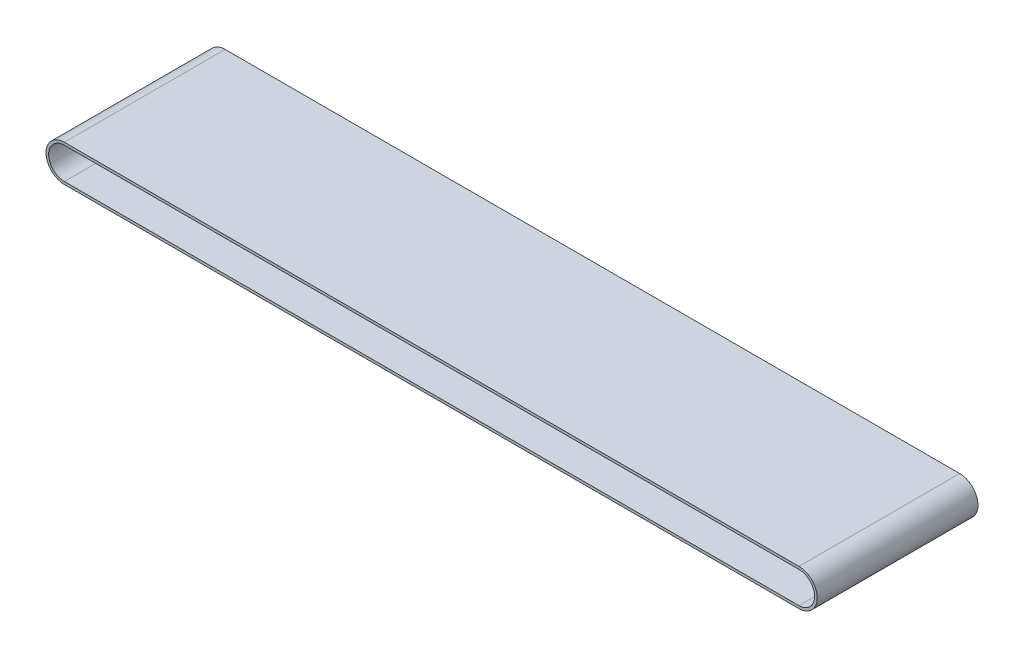
SolidWorks part; units mm, degrees
ref_plane "Front Plane" through (0, 0, 0) normal (0, 0, 1) x (1, 0, 0)
ref_plane "Top Plane" through (0, 0, 0) normal (0, 1, 0) x (1, 0, 0)
ref_plane "Right Plane" through (0, 0, 0) normal (1, 0, 0) x (0, 0, -1)
sketch "Sketch1" plane through (0, 0, 0) normal (0, 0, 1) x (1, 0, 0)
  line L202 (0, 61.4422) -> (0, -79.0701) construction
  line L203 (-281, 0) -> (281, 0) construction
  line L204 (-281, 12) -> (281, 12)
  line L205 (-281, -12) -> (281, -12)
  line L206 (-281, 0) -> (281, 0) construction
  line L207 (-281, 14) -> (281, 14)
  line L208 (-281, -14) -> (281, -14)
  arc A0 (-281, 12) -> (-281, -12) centre (-281, 0) ccw
  arc A1 (281, -12) -> (281, 12) centre (281, 0) ccw
  arc A2 (-281, 14) -> (-281, -14) centre (-281, 0) ccw
  arc A3 (281, -14) -> (281, 14) centre (281, 0) ccw
  point P4 (0, 0)
  point P11 (0, 0)
  point P16 (-295, 0)
  point P17 (295, 0)
  point P18 (-293, 0)
  dimension "D2" = 2
  dimension "D1" = 590
  dimension "D3" = 12
  dimension "D4" = 2
extrude "Boss-Extrude1" add sketch "Sketch1" along normal blind 123
